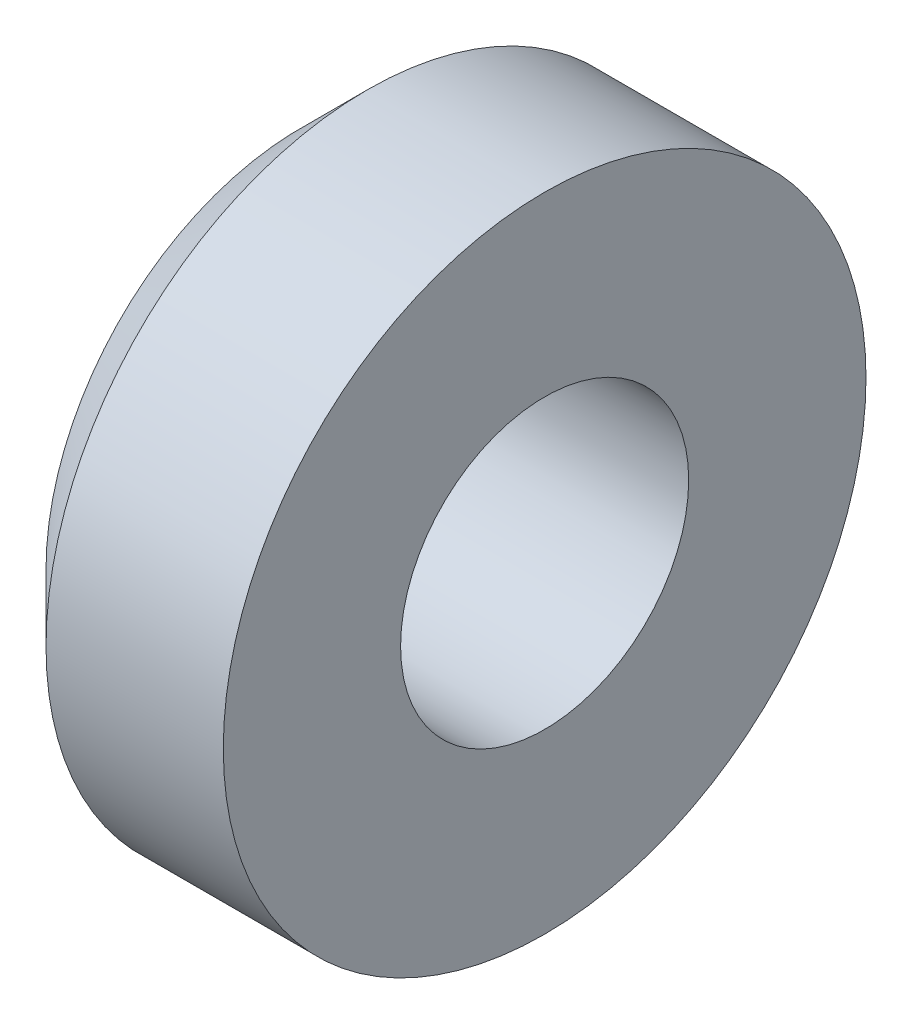
SolidWorks part; units mm, degrees
ref_plane "Front Plane" through (0, 0, 0) normal (0, 0, 1) x (1, 0, 0)
ref_plane "Top Plane" through (0, 0, 0) normal (0, 1, 0) x (1, 0, 0)
ref_plane "Right Plane" through (0, 0, 0) normal (1, 0, 0) x (0, 0, -1)
sketch "Sketch1" plane through (0, 0, 0) normal (0, 0, 1) x (1, 0, 0)
  line L0 (0, 2.875) -> (0.75, 3.625)
  line L1 (0.75, 3.625) -> (2.75, 3.625)
  line L2 (0, 2.875) -> (0, 1.625)
  line L3 (0, 1.625) -> (2.75, 1.625)
  line L4 (2.75, 1.625) -> (2.75, 3.625)
  line L5 (-4.995, 0) -> (4.7956, 0) construction
  line L6 (0, 1.625) -> (0, 0) construction
  dimension "D1" = 2.75
  dimension "D2" = 45
  dimension "D3" = 2
  dimension "D4" = 5.75
  dimension "D5" = 3.25
revolve "Revolve1" add sketch "Sketch1" angle 360 about L5
equation "\"D2@Sketch1\" = \"D1@Sketch1\" / 2.5"
